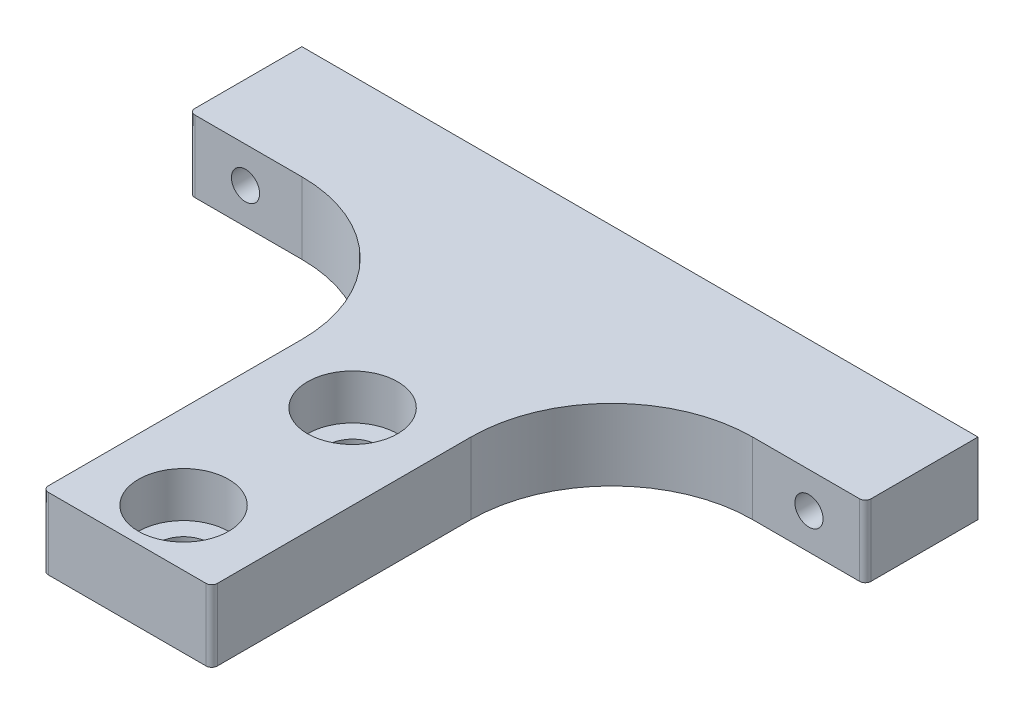
SolidWorks part; units mm, degrees
material "6061-T6 (SS)"
ref_plane "Front Plane" through (0, 0, 0) normal (0, 0, 1) x (1, 0, 0)
ref_plane "Top Plane" through (0, 0, 0) normal (0, 1, 0) x (1, 0, 0)
ref_plane "Right Plane" through (0, 0, 0) normal (1, 0, 0) x (0, 0, -1)
sketch "Sketch2" plane through (0, 0, 0) normal (0, 1, 0) x (1, 0, 0)
  line L0 (-30, 0) -> (30, 0)
  line L1 (-30, 0) -> (-30, -10)
  line L2 (-30, -10) -> (-7.5, -10)
  line L3 (-7.5, -10) -> (-7.5, -45.5)
  line L4 (-7.5, -45.5) -> (7.5, -45.5)
  line L5 (0, 0) -> (0, -45.5) construction
  line L6 (7.5, -10) -> (7.5, -45.5)
  line L7 (30, -10) -> (7.5, -10)
  line L8 (30, 0) -> (30, -10)
  point P4 (0, 0)
  dimension "D1" = 60
  dimension "D2" = 15
  dimension "D3" = 45.5
  dimension "D4" = 10
extrude "Boss-Extrude1" add sketch "Sketch2" along normal blind 6.35
fillet "Fillet1" radius 12.5 2 edges at (7.5, 3.175, 10) (-7.5, 3.175, 10)
sketch "Sketch3" plane through (0, 6.35, 0) normal (0, 1, 0) x (1, 0, 0)
  line L0 (-7.5, -20.5) -> (7.5, -20.5) construction
  line L1 (-7.5, -22.5) -> (-7.5, -45.5) construction
  line L2 (7.5, -45.5) -> (7.5, -22.5) construction
  line L3 (-7.5, -45.5) -> (7.5, -45.5) construction
  line L4 (0, -20.5) -> (0, -45.5) construction
  line L5 (0, -33) -> (10.8574, -33) construction
  point P12 (0, -25.5)
  point P13 (0, -40.5)
  dimension "D1" = 25
  dimension "D2" = 15
hole_wizard "CBORE for M4 SHCS1" positions "Sketch3" profile "Sketch4" counterbore size "M4" standard "ANSI Metric" end condition through all
sketch "Sketch4" plane through (0, 6.35, 40.5) normal (1, 0, 0) x (0, 0, 1)
  line L0 (0, 0) -> (0, 6.35)
  line L1 (0, 6.35) -> (2.25, 6.35)
  line L3 (2.25, 6.35) -> (2.25, 4)
  line L4 (2.25, 4) -> (4, 4)
  line L5 (4, 4) -> (4, 0)
  line L7 (4, 0) -> (0, 0)
  line L11 (0, -6.35) -> (0, 107.95) construction
  dimension "Thru Hole Dia." = 4.5
  dimension "Thru Hole Depth" = 6.35
  dimension "C'Bore Dia." = 8
  dimension "C'Bore Depth" = 4
sketch "Sketch5" plane through (0, 0, 0) normal (0, 0, -1) x (-1, 0, 0)
  line L0 (-30, 3.175) -> (30, 3.175) construction
  line L1 (-30, 6.35) -> (-30, 0) construction
  line L2 (30, 6.35) -> (30, 0) construction
  line L3 (0, 0) -> (0, 6.35) construction
  line L4 (-30, 6.35) -> (30, 6.35) construction
  point P6 (25, 3.175)
  point P12 (-25, 3.175)
  dimension "D1" = 5
hole_wizard "M3x0.5 Tapped Hole1" positions "Sketch5" profile "Sketch6" tap size "M3x0.5" standard "ANSI Metric" end condition up to next
sketch "Sketch6" plane through (25, 3.175, 0) normal (1, 0, 0) x (0, 1, 0)
  line L0 (0, 0) -> (0, 10)
  line L1 (0, 10) -> (1.25, 10)
  line L2 (1.25, 10) -> (1.25, 0)
  line L5 (1.25, 0) -> (0, 0)
  line L11 (0, -6.35) -> (0, 107.95) construction
  dimension "Thru Tap Drill Dia." = 2.5
  dimension "Thru Tap Drill Depth" = 10
fillet "Fillet2" radius 0.5 2 edges at (30, 3.175, 10) (-30, 3.175, 10)
fillet "Fillet3" radius 0.5 2 edges at (7.5, 3.175, 45.5) (-7.5, 3.175, 45.5)
split line "Split Line2"
equation "\"D3@Sketch2\"=40.50+5.00"
